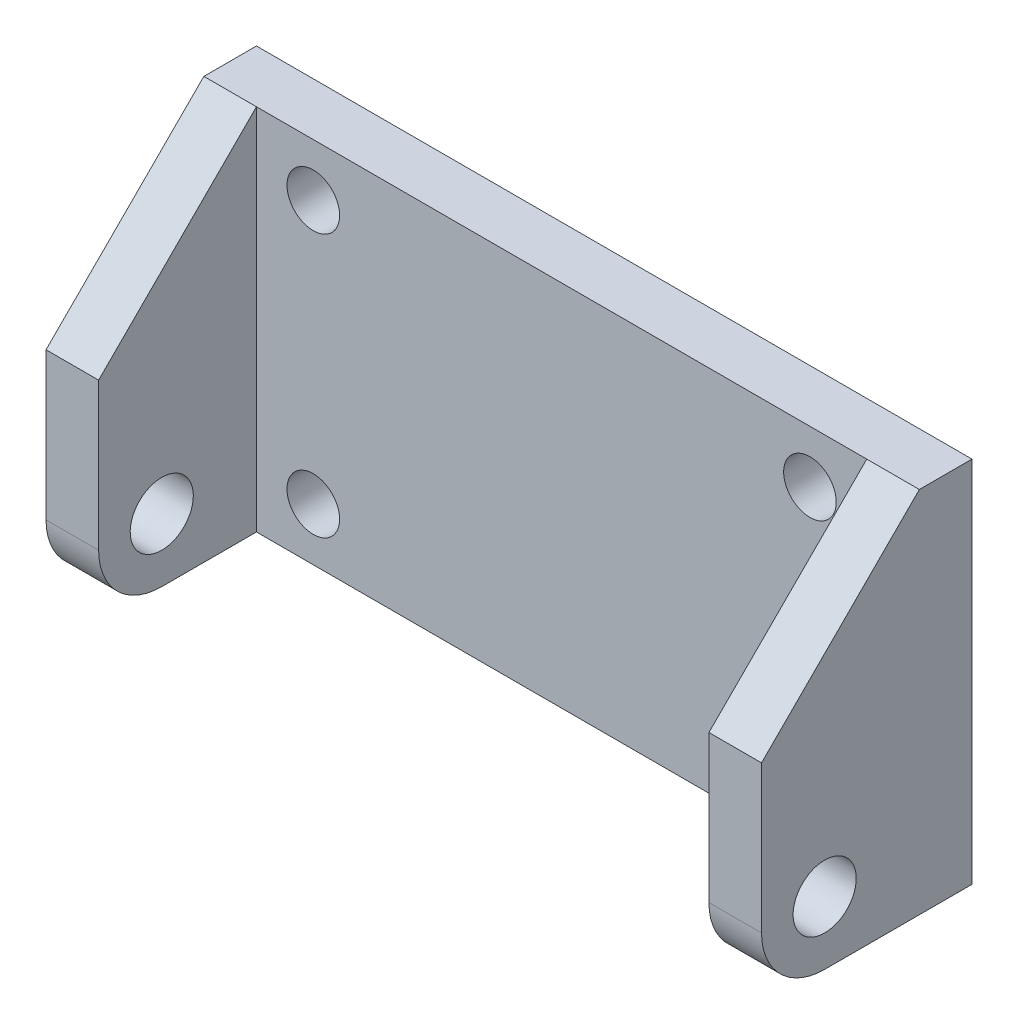
SolidWorks part; units mm, degrees
ref_plane "Front Plane" through (0, 0, 0) normal (0, 0, 1) x (1, 0, 0)
ref_plane "Top Plane" through (0, 0, 0) normal (0, 1, 0) x (1, 0, 0)
ref_plane "Right Plane" through (0, 0, 0) normal (1, 0, 0) x (0, 0, -1)
sketch "Sketch1" plane through (0, 0, 0) normal (0, 0, 1) x (1, 0, 0)
  line L1 (-16.3786, 12.8871) -> (17.6214, 12.8871)
  line L2 (-16.3786, 12.8871) -> (-16.3786, -4.6129)
  line L3 (-16.3786, -4.6129) -> (17.6214, -4.6129)
  line L4 (17.6214, 12.8871) -> (17.6214, -4.6129)
  circle A0 centre (-11.1786, -2.1129) radius 1.25
  circle A1 centre (12.4214, -2.1129) radius 1.25
  circle A2 centre (12.4214, 10.3871) radius 1.25
  circle A3 centre (-11.1786, 10.3871) radius 1.25
  point P6 (0.6214, -4.6129)
  point P8 (0, 0)
  point P9 (0, 0)
  point P15 (0, 0)
  point P16 (0, 0)
  point P17 (0, 0)
  dimension "D3" = 2.5
  dimension "D1" = 11.8
  dimension "D2" = 12.5
  dimension "D4" = 2.5
  dimension "D5" = 11.8
  dimension "D8" = 2.5
  dimension "D9" = 34
  dimension "D6" = 2
  dimension "D7" = 2
extrude "Boss-Extrude1" add sketch "Sketch1" along normal blind 2.5
sketch "Sketch2" plane through (0, 0, 2.5) normal (0, 0, 1) x (1, 0, 0)
  line L0 (17.6214, 12.8871) -> (-16.3786, 12.8871) construction
  line L1 (-16.3786, -4.6129) -> (-13.8786, -4.6129)
  line L2 (-16.3786, -4.6129) -> (-16.3786, 12.8871)
  line L3 (-16.3786, 12.8871) -> (-13.8786, 12.8871)
  line L4 (-13.8786, -4.6129) -> (-13.8786, 12.8871)
  line L6 (17.6214, -4.6129) -> (15.1214, -4.6129)
  line L7 (17.6214, -4.6129) -> (17.6214, 12.8871)
  line L8 (17.6214, 12.8871) -> (15.1214, 12.8871)
  line L9 (15.1214, -4.6129) -> (15.1214, 12.8871)
  dimension "D1" = 2.5
  dimension "D2" = 2.5
extrude "Boss-Extrude2" add sketch "Sketch2" along normal blind 7.5
chamfer "Chamfer1" distance 7.5 angle 45 2 edges at (16.3714, 12.8871, 10) (-15.1286, 12.8871, 10)
fillet "Fillet1" radius 3 2 edges at (16.3714, -4.6129, 10) (-15.1286, -4.6129, 10)
sketch "Sketch3" plane through (17.6214, 0, 0) normal (1, 0, 0) x (0, 0, -1)
  line L0 (-7, -4.6129) -> (0, -4.6129) construction
  line L1 (-10, -1.6129) -> (-10, 5.3871) construction
  circle A0 centre (-7, -1.6129) radius 1.5
  dimension "D1" = 3
  dimension "D2" = 3
  dimension "D3" = 3
extrude "Cut-Extrude1" cut sketch "Sketch3" against normal through all
